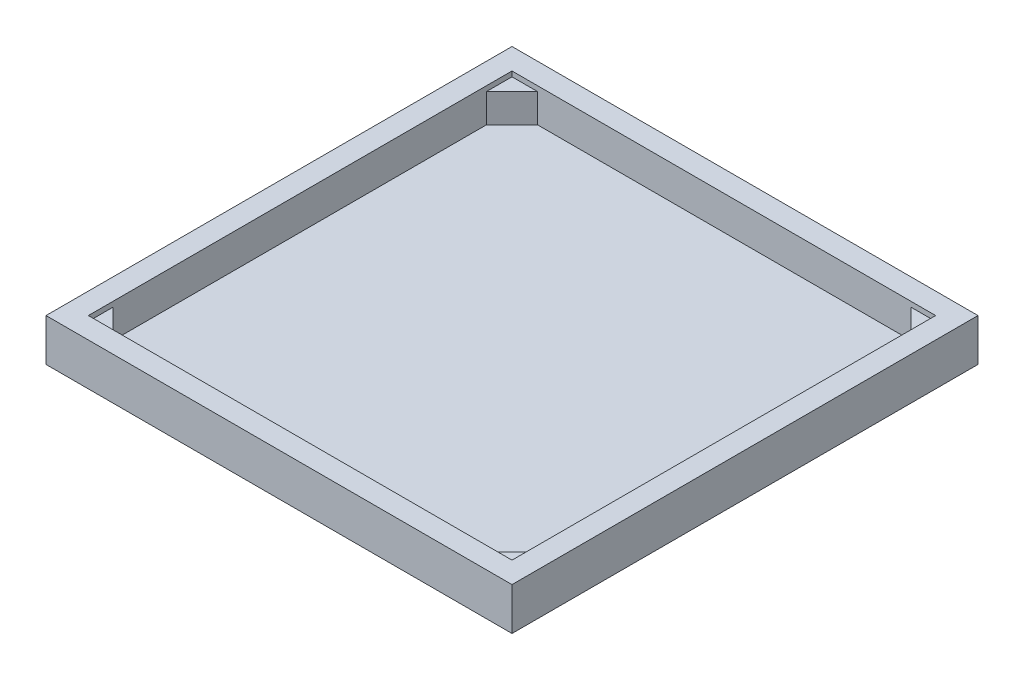
SolidWorks part; units mm, degrees
ref_plane "Ebene vorne" through (0, 0, 0) normal (0, 0, 1) x (1, 0, 0)
ref_plane "Ebene oben" through (0, 0, 0) normal (0, 1, 0) x (1, 0, 0)
ref_plane "Ebene rechts" through (0, 0, 0) normal (1, 0, 0) x (0, 0, -1)
sketch "Sketch1" plane through (0, 0, 0) normal (0, 1, 0) x (1, 0, 0)
  line L1 (-275, -275) -> (275, -275)
  line L2 (-275, -275) -> (-275, 275)
  line L3 (-275, 275) -> (275, 275)
  line L4 (275, -275) -> (275, 275)
  line L5 (-275, -275) -> (275, 275) construction
  line L6 (-275, 275) -> (275, -275) construction
  point P0 (0, 0)
  dimension "D1" = 550
  dimension "D2" = 550
extrude "Boss-Extrude1" add sketch "Sketch1" along normal blind 50
sketch "Sketch2" plane through (0, 50, 0) normal (0, 1, 0) x (1, 0, 0)
  line L1 (-250, -250) -> (250, -250)
  line L2 (-250, -250) -> (-250, 250)
  line L3 (-250, 250) -> (250, 250)
  line L4 (250, -250) -> (250, 250)
  line L5 (-250, -250) -> (250, 250) construction
  line L6 (-250, 250) -> (250, -250) construction
  point P0 (0, 0)
  dimension "D1" = 500
  dimension "D2" = 500
extrude "Cut-Extrude1" cut sketch "Sketch2" against normal blind 40 contours L2 L3 L4 L1
sketch "Sketch3" plane through (0, 10, 0) normal (0, 1, 0) x (1, 0, 0)
  line L0 (-250, 250) -> (-220, 250)
  line L1 (-250, 250) -> (250, 250) construction
  line L2 (-250, 250) -> (-250, 220)
  line L3 (-250, -250) -> (-250, 250) construction
  line L4 (-250, 220) -> (-220, 250)
extrude "Boss-Extrude2" add sketch "Sketch3" along normal blind 34 contours L4 L0 L2
pattern_circular "CirPattern1" count 4 over 360 about axis through (0.4328, 0, 0.4328) along (0, 1, 0) of "Boss-Extrude2"
